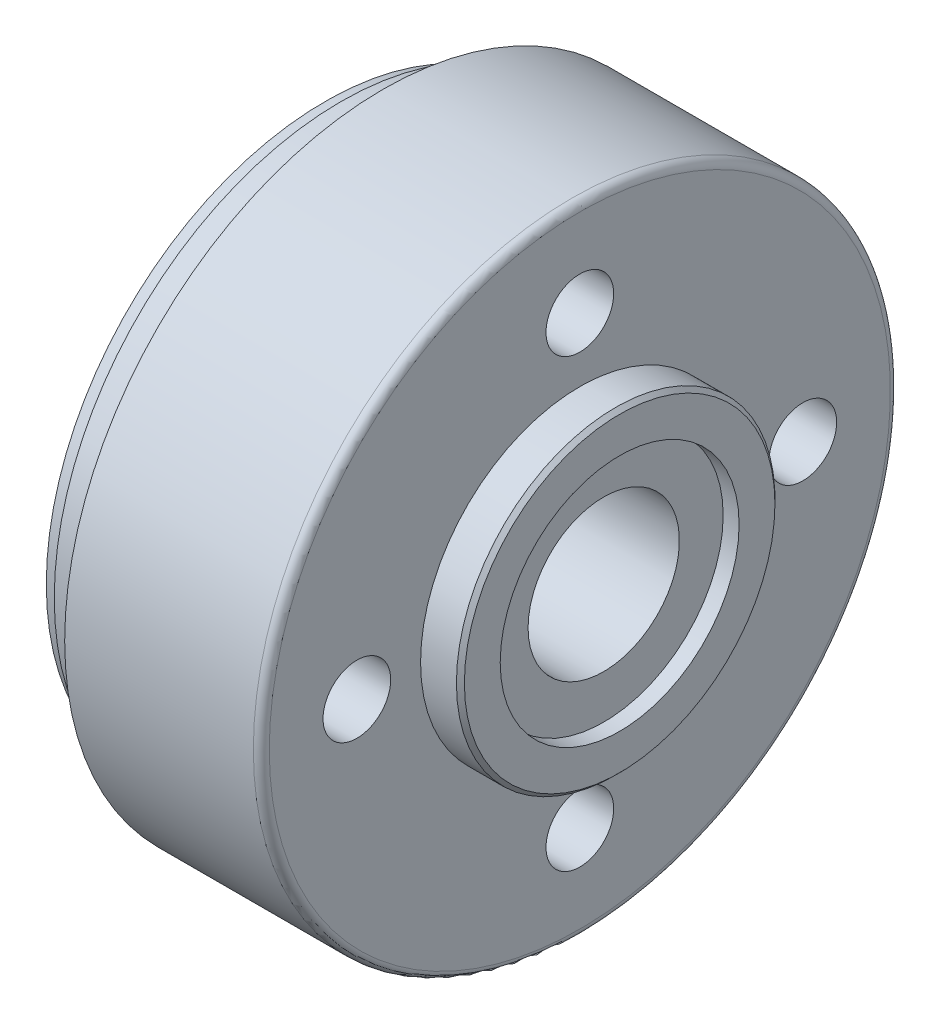
SolidWorks part; units mm, degrees
ref_plane "Front" through (0, 0, 0) normal (0, 0, 1) x (1, 0, 0)
ref_plane "Top" through (0, 0, 0) normal (0, 1, 0) x (1, 0, 0)
ref_plane "Right" through (0, 0, 0) normal (1, 0, 0) x (0, 0, -1)
sketch "Sketch1" plane through (0, 0, 0) normal (0, 0, 1) x (1, 0, 0)
  line L0 (-31.2769, 0) -> (34.1365, 0) construction
  line L1 (0, 9.5) -> (35, 9.5)
  line L2 (35, 9.5) -> (35, 15)
  line L3 (35, 15) -> (37, 15)
  line L4 (37, 15) -> (37, 20)
  line L5 (37, 20) -> (32, 20)
  line L6 (32, 20) -> (32, 40)
  line L7 (32, 40) -> (7.3094, 40)
  line L8 (7.3094, 40) -> (5, 36)
  line L9 (5, 36) -> (2, 36)
  line L10 (2, 36) -> (2, 35)
  line L11 (2, 35) -> (0, 35)
  line L12 (0, 35) -> (0, 9.5)
  dimension "D1" = 37
  dimension "D2" = 5
  dimension "D3" = 19
  dimension "D4" = 2
  dimension "D5" = 3
  dimension "D6" = 30
  dimension "D7" = 70
  dimension "D8" = 30
  dimension "D9" = 40
  dimension "D10" = 80
  dimension "D11" = 72
  dimension "D12" = 2
revolve "Base-Revolve" add sketch "Sketch1" angle 360 about L0
cosmetic thread "Cosmetic Thread5" parameters "D1"=15, "D2"=20.995
sketch "Sketch2" [suppressed] plane through (32, 0, 0) normal (1, 0, 0) x (0, 0, -1)
  line L0 (-64.4324, 0) -> (54.956, 0) construction
  line L1 (0, 59.3368) -> (0, -51.4728) construction
  line L2 (-36.2711, -36.2711) -> (0, 0) construction
  circle A0 centre (0, 0) radius 28 construction
  circle A1 centre (0, 28) radius 4.25
  circle A2 centre (0, -28) radius 4.25
  circle A3 centre (28, 0) radius 4.25
  circle A4 centre (-28, 0) radius 4.25
  dimension "D2" = 56
  dimension "D3" = 8.5
  dimension "D1" = 45
chamfer "Rejfning 0,5 x 45 gr." distance 0.5 angle 45 1 edges at (37, 0, 20)
fillet "Runding R1" radius 1 1 edges at (32, 0, 40)
hole_wizard "Hole1" positions "Sketch4" profile "Sketch3" legacy
sketch "Sketch4" plane through (32, 0, 0) normal (1, 0, 0) x (0, 0, -1)
  circle A1 centre (0, 0) radius 28 construction
  point P0 (0, 28)
  point P3 (-28, 0)
  point P4 (0, -28)
  point P5 (28, 0)
  dimension "D1" = 56
sketch "Sketch3" plane through (32, 28, 0) normal (0, 1, 0) x (0, 0, -1)
  line L0 (0, 0) -> (0, 20.0537)
  line L1 (0, 20.0537) -> (4.25, 17.5)
  line L2 (4.25, 17.5) -> (4.25, 0)
  line L4 (4.25, 0) -> (0, 0)
  line L6 (0, 20.0537) -> (-4.25, 17.5) construction
  line L7 (0, -4.2442) -> (0, 117.3081) construction
  dimension "Diameter" = 8.5
  dimension "Depth" = 17.5
  dimension "Drill Angle" = 118
cosmetic thread "Cosmetic Thread6" parameters "D1"=15, "D2"=10
cosmetic thread "Cosmetic Thread7" parameters "D1"=15, "D2"=10
cosmetic thread "Cosmetic Thread8" parameters "D1"=15, "D2"=10
cosmetic thread "Cosmetic Thread9" parameters "D1"=15, "D2"=10
